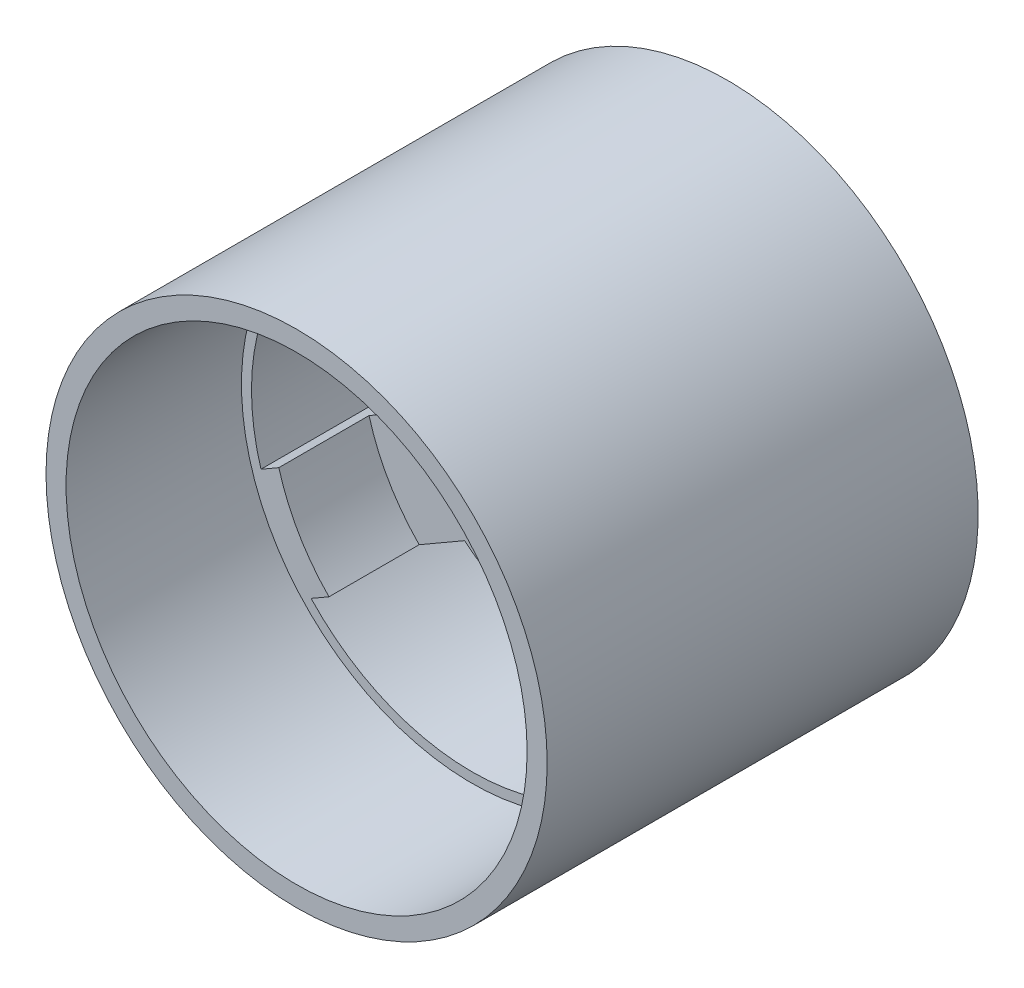
SolidWorks part; units mm, degrees
ref_plane "前视基准面" through (0, 0, 0) normal (0, 0, 1) x (1, 0, 0)
ref_plane "上视基准面" through (0, 0, 0) normal (0, 1, 0) x (1, 0, 0)
ref_plane "右视基准面" through (0, 0, 0) normal (1, 0, 0) x (0, 0, -1)
sketch "草图1" plane through (0, 0, 0) normal (0, 0, 1) x (1, 0, 0)
  circle A0 centre (0, 0) radius 22
  circle A1 centre (0, 0) radius 17
extrude "凸台-拉伸1" add sketch "草图1" along normal blind 9
sketch "草图2" plane through (0, 0, 0) normal (0, 0, -1) x (-1, 0, 0)
  circle A0 centre (0, 0) radius 22
extrude "凸台-拉伸2" add sketch "草图2" along normal blind 3
sketch "草图3" plane through (0, 0, -3) normal (0, 0, -1) x (-1, 0, 0)
  circle A1 centre (0, 10) radius 1
  circle A2 centre (8.6603, -5) radius 1
  circle A3 centre (-8.6603, -5) radius 1
  point P12 (0, 0)
  dimension "D1" = 3
extrude "切除-拉伸1" cut sketch "草图3" against normal blind 3
sketch "草图4" plane through (0, 0, -3) normal (0, 0, -1) x (-1, 0, 0)
  line L1 (24.7877, -8.5377) -> (5, 2.8868)
  line L2 (5, 15) -> (5, 2.8868)
  line L3 (-6.1603, -9.3301) -> (0, -5.7735)
  line L4 (19.7877, -17.1979) -> (0, -5.7735)
  line L5 (-5, 10) -> (-5, 2.8868)
  line L9 (-5, 2.8868) -> (-28.9027, -10.9135)
  line L16 (-6.1603, -9.3301) -> (-23.9027, -19.5738)
  line L19 (-5, 10) -> (-5, 31.0066)
  line L21 (5, 31.0066) -> (5, 15)
  line L22 (5, 31.0066) -> (28.5963, 19.5438)
  line L23 (28.5963, 19.5438) -> (24.7877, -8.5377)
  line L24 (19.7877, -17.1979) -> (-4.0351, -32.4361)
  line L25 (-4.0351, -32.4361) -> (-23.9027, -19.5738)
  line L26 (-28.9027, -10.9135) -> (-27.6381, 27.1706)
  line L27 (-27.6381, 27.1706) -> (-5, 31.0066)
extrude "切除-拉伸2" cut sketch "草图4" against normal blind 25
sketch "草图5" plane through (0, 0, -3) normal (0, 0, -1) x (-1, 0, 0)
  circle A0 centre (0, 0) radius 4
extrude "切除-拉伸3" cut sketch "草图5" against normal blind 10
fillet "圆角1" radius 10 1 edges at (-5, 2.8868, -1.5)
fillet "圆角2" radius 10 2 edges at (5, 2.8868, -1.5) (0, -5.7735, -1.5)
sketch "草图7" plane through (0, 0, -3) normal (0, 0, -1) x (-1, 0, 0)
  circle A0 centre (0, 0) radius 25
  circle A1 centre (0, 0) radius 22
extrude "凸台-拉伸3" add sketch "草图7" against normal blind 30
sketch "草图8" plane through (0, 0, -3) normal (0, 0, -1) x (-1, 0, 0)
  line L0 (-21.054, -6.382) -> (-15.7536, -3.3218)
  line L2 (16.054, -15.0423) -> (10.7536, -11.9821)
  line L3 (16.054, -15.0423) -> (5, -8.6603) construction
  line L4 (-16.054, -15.0423) -> (-10.7536, -11.9821)
  line L6 (21.054, -6.382) -> (15.7536, -3.3218)
  line L8 (5, 21.4243) -> (5, 15.3039)
  line L10 (-5, 21.4243) -> (-5, 15.3039)
  arc A0 (5, 15.3039) -> (-5, 15.3039) centre (0, 0) ccw
  arc A1 (16.054, -15.0423) -> (21.054, -6.382) centre (0, 0) ccw
  arc A2 (5, 21.4243) -> (-5, 21.4243) centre (0, 0) ccw
  arc A3 (-21.054, -6.382) -> (-16.054, -15.0423) centre (0, 0) ccw
  arc A4 (-15.7536, -3.3218) -> (-10.7536, -11.9821) centre (0, 0) ccw
  arc A5 (10.7536, -11.9821) -> (15.7536, -3.3218) centre (0, 0) ccw
extrude "凸台-拉伸4" add sketch "草图8" along normal blind 4
sketch "草图9" plane through (0, 0, -7) normal (0, 0, -1) x (-1, 0, 0)
  circle A0 centre (0, 0) radius 38.6725
extrude "切除-拉伸4" cut sketch "草图9" against normal blind 1
sketch "草图10" plane through (0, 0, -3) normal (0, 0, -1) x (-1, 0, 0)
  circle A0 centre (0, 0) radius 22
  circle A1 centre (0, 0) radius 25
extrude "凸台-拉伸5" add sketch "草图10" along normal blind 13.5
sketch "草图11" plane through (0, 0, -16.5) normal (0, 0, -1) x (-1, 0, 0)
  circle A0 centre (0, 0) radius 23
extrude "切除-拉伸5" cut sketch "草图11" against normal blind 10.5
chamfer "倒角2" distance 1 angle 45 1 edges at (-23, 0, -16.5)
sketch "草图12" plane through (0, 0, 27) normal (0, 0, 1) x (1, 0, 0)
  circle A0 centre (0, 0) radius 23
extrude "切除-拉伸6" cut sketch "草图12" against normal blind 18
sketch "草图13" plane through (0, 0, 27) normal (0, 0, 1) x (1, 0, 0)
  circle A0 centre (0, 0) radius 39.8309
extrude "切除-拉伸7" cut sketch "草图13" against normal blind 2.5
sketch "草图14" plane through (0, 0, -3) normal (0, 0, -1) x (-1, 0, 0)
  circle A0 centre (0, 0) radius 15
extrude "切除-拉伸8" cut sketch "草图14" against normal blind 0.5
sketch "草图15" plane through (0, 0, 24.5) normal (0, 0, 1) x (1, 0, 0)
  circle A0 centre (0, 0) radius 23
  circle A1 centre (0, 0) radius 25
extrude "凸台-拉伸6" add sketch "草图15" along normal blind 2
sketch "草图16" plane through (0, 0, 9) normal (0, 0, 1) x (1, 0, 0)
  circle A0 centre (0, 0) radius 20
extrude "切除-拉伸9" cut sketch "草图16" against normal blind 9
sketch "草图17" plane through (0, 0, 0) normal (0, 0, 1) x (1, 0, 0)
  circle A0 centre (0, 0) radius 20
  circle A1 centre (8.6603, -5) radius 1
  circle A2 centre (-8.6603, -5) radius 1
  circle A3 centre (0, 10) radius 1
  circle A4 centre (0, 0) radius 4
extrude "凸台-拉伸7" add sketch "草图17" against normal blind 2.5
sketch "草图18" plane through (0, 0, -2.5) normal (0, 0, -1) x (-1, 0, 0)
  circle A1 centre (-6.926, -4.0038) radius 1.5
  circle A2 centre (-4.0038, 6.926) radius 1.5
  circle A3 centre (6.926, 4.0038) radius 1.5
  circle A4 centre (4.0038, -6.926) radius 1.5
  point P13 (0, 0)
  dimension "D1" = 4
extrude "切除-拉伸10" cut sketch "草图18" against normal blind 21.5
sketch "草图19" plane through (0, 0, -2.5) normal (0, 0, -1) x (-1, 0, 0)
  line L0 (-19.9863, -5.7656) -> (-14.7407, -2.737)
  line L1 (-5, 20.1914) -> (-5, 14.1343)
  line L2 (5, 20.1914) -> (5, 14.1343)
  line L3 (19.9863, -5.7656) -> (14.7407, -2.737)
  line L4 (14.9863, -14.4258) -> (9.7407, -11.3973)
  line L5 (-14.9863, -14.4258) -> (-9.7407, -11.3973)
  arc A0 (-5, 14.1343) -> (-14.7407, -2.737) centre (0, 0) ccw
  arc A1 (-5, 20.1914) -> (-19.9863, -5.7656) centre (0, 0) ccw
  arc A2 (19.9863, -5.7656) -> (5, 20.1914) centre (0, 0) ccw
  arc A3 (14.7407, -2.737) -> (5, 14.1343) centre (0, 0) ccw
  arc A4 (-14.9863, -14.4258) -> (14.9863, -14.4258) centre (0, 0) ccw
  arc A5 (-9.7407, -11.3973) -> (9.7407, -11.3973) centre (0, 0) ccw
  point P16 (0, 0)
  dimension "D1" = 3
extrude "切除-拉伸11" cut sketch "草图19" against normal blind 21.5
